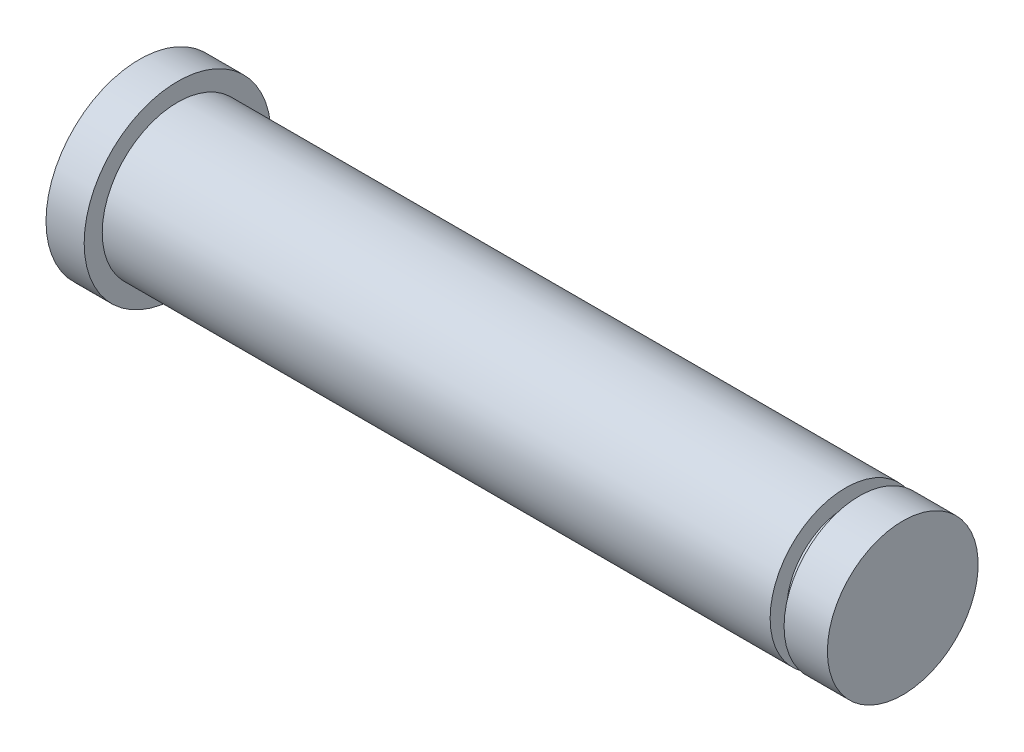
SolidWorks part; units mm, degrees
material "Stainless Steel (ferritic)"
ref_plane "Front" through (0, 0, 0) normal (0, 0, 1) x (1, 0, 0)
ref_plane "Top" through (0, 0, 0) normal (0, 1, 0) x (1, 0, 0)
ref_plane "Right" through (0, 0, 0) normal (1, 0, 0) x (0, 0, -1)
sketch "Sketch1" plane through (0, 0, 0) normal (0, 0, 1) x (1, 0, 0)
  line L0 (0, 0) -> (66.4337, 0) construction
  line L1 (0, 0) -> (0, 4.8966)
  line L2 (0, 4.8966) -> (2, 4.8966)
  line L3 (2, 4.8966) -> (2, 3.95)
  line L4 (2, 3.95) -> (37, 3.95)
  line L5 (37, 3.95) -> (37, 3.08)
  line L6 (37, 3.08) -> (37.73, 3.08)
  line L7 (37.73, 3.08) -> (37.73, 3.95)
  line L8 (37.73, 3.95) -> (40, 3.95)
  line L9 (40, 3.95) -> (40, 0)
  line L10 (0, 0) -> (40, 0)
  dimension "D2" = 7.9
  dimension "D3" = 2
  dimension "D4" = 0.73
  dimension "D5" = 6.16
  dimension "D6" = 35
  dimension "D7" = 40
revolve "Revolve1" add sketch "Sketch1" angle 360 about L0
